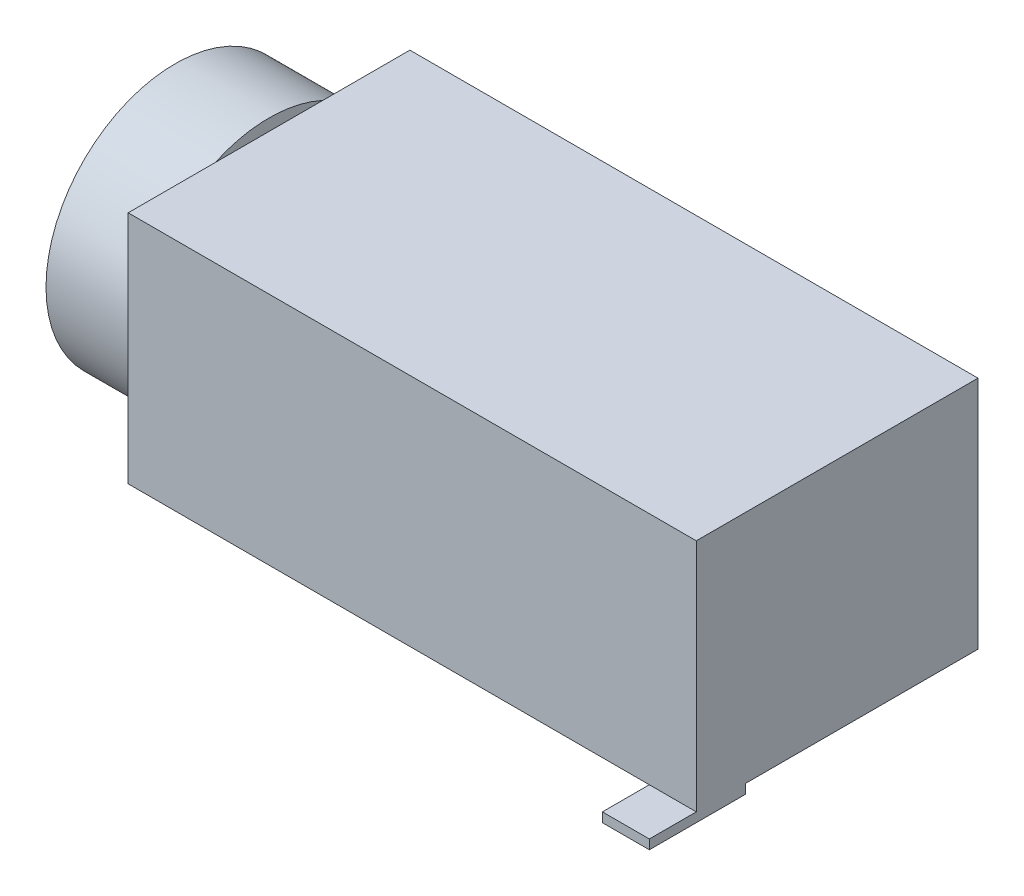
SolidWorks part; units mm, degrees
ref_plane "Front Plane" through (0, 0, 0) normal (0, 0, 1) x (1, 0, 0)
ref_plane "Top Plane" through (0, 0, 0) normal (0, 1, 0) x (1, 0, 0)
ref_plane "Right Plane" through (0, 0, 0) normal (1, 0, 0) x (0, 0, -1)
sketch "Sketch1" plane through (0, 0, 0) normal (0, 1, 0) x (1, 0, 0)
  line L1 (6.05, 3) -> (-6.05, 3)
  line L2 (6.05, 3) -> (6.05, -3)
  line L3 (6.05, -3) -> (-6.05, -3)
  line L4 (-6.05, 3) -> (-6.05, -3)
  line L5 (6.05, 3) -> (-6.05, -3) construction
  line L6 (6.05, -3) -> (-6.05, 3) construction
  point P0 (0, 0)
  dimension "D1" = 12.1
  dimension "D2" = 6
extrude "Boss-Extrude1" add sketch "Sketch1" along normal mid plane 5
sketch "Sketch2" plane through (-6.05, 0, 0) normal (-1, 0, 0) x (0, 0, 1)
  circle A0 centre (0, 0) radius 2.75
  circle A1 centre (0, 0) radius 1.8
  dimension "D1" = 5.5
extrude "Boss-Extrude2" add sketch "Sketch2" along normal blind 2
sketch "Sketch3" plane through (0, -2.5, 0) normal (0, -1, 0) x (1, 0, 0)
  line L0 (-8.05, 2.75) -> (-8.05, -2.75) construction
  circle A0 centre (-4.25, 0) radius 0.6
  circle A1 centre (2.75, 0) radius 0.6
  dimension "D1" = 1.2
  dimension "D2" = 3.8
  dimension "D3" = 7
extrude "Boss-Extrude3" add sketch "Sketch3" along normal blind 0.8
fillet "Fillet1" radius 0.2 2 edges at (2.75, -3.3, -0.6) (-4.25, -3.3, -0.6)
sketch "Sketch4" plane through (0, -2.5, 0) normal (0, -1, 0) x (1, 0, 0)
  line L0 (-2.95, -2.1958) -> (-2.95, -4.0221) construction
  line L1 (-8.05, 2.75) -> (-8.05, -2.75) construction
  line L2 (0.05, -2.1958) -> (0.05, -4.0221) construction
  line L3 (4.05, -2.1958) -> (4.05, -4.0221) construction
  line L4 (-3.45, -1.5397) -> (-3.45, -4)
  line L5 (-0.45, -1.5397) -> (-0.45, -4)
  line L6 (3.55, -1.5397) -> (3.55, -4)
  line L7 (-2.45, -1.5397) -> (-2.45, -4)
  line L8 (0.55, -1.5397) -> (0.55, -4)
  line L9 (4.55, -1.5397) -> (4.55, -4)
  line L10 (5.55, 3.7143) -> (5.55, 1.5391) construction
  line L11 (5.05, 4) -> (5.05, 1.9525)
  line L12 (6.05, 4) -> (6.05, 1.9525)
  line L13 (-9.4058, 0) -> (9.9348, 0) construction
  line L14 (-3.45, -4) -> (-2.45, -4)
  line L15 (5.05, 4) -> (6.05, 4)
  line L16 (6.05, 3.7143) -> (6.05, 1.5391) construction
  line L17 (5.05, 3.7143) -> (5.05, 1.5391) construction
  line L18 (-3.45, -2.1958) -> (-3.45, -4.0221) construction
  line L19 (-2.45, -2.1958) -> (-2.45, -4.0221) construction
  line L20 (-9.4058, -4) -> (9.9348, -4) construction
  line L21 (-0.45, -4) -> (0.55, -4)
  line L22 (3.55, -4) -> (4.55, -4)
  line L23 (-9.4058, 4) -> (9.9348, 4) construction
  line L24 (-0.45, -2.1958) -> (-0.45, -4.0221) construction
  line L25 (0.55, -2.1958) -> (0.55, -4.0221) construction
  line L26 (3.55, -2.1958) -> (3.55, -4.0221) construction
  line L27 (4.55, -2.1958) -> (4.55, -4.0221) construction
  line L28 (-3.45, -1.5397) -> (-2.45, -1.5397)
  line L29 (5.05, 1.9525) -> (6.05, 1.9525)
  line L30 (-0.45, -1.5397) -> (0.55, -1.5397)
  line L31 (3.55, -1.5397) -> (4.55, -1.5397)
  dimension "D1" = 5.1
  dimension "D6" = 13.6
  dimension "D2" = 3
  dimension "D3" = 4
  dimension "D7" = 0.5
  dimension "D8" = 0.5
  dimension "D9" = 4
  dimension "D10" = 4
extrude "Boss-Extrude4" add sketch "Sketch4" along normal blind 0.2
